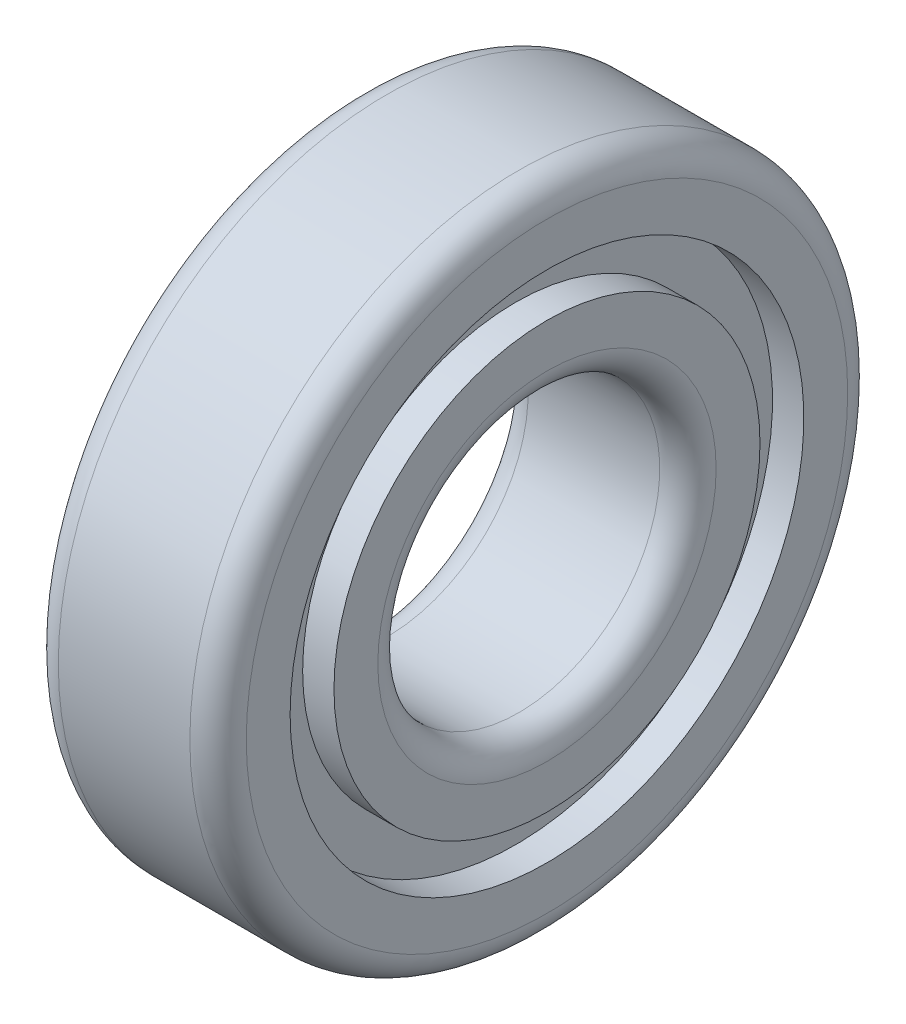
SolidWorks part; units mm, degrees
material "AISI 1020"
ref_plane "Спереди" through (0, 0, 0) normal (0, 0, 1) x (1, 0, 0)
ref_plane "Сверху" through (0, 0, 0) normal (0, 1, 0) x (1, 0, 0)
ref_plane "Справа" through (0, 0, 0) normal (1, 0, 0) x (0, 0, -1)
sketch "Эскиз1" plane through (0, 0, 0) normal (0, 0, 1) x (1, 0, 0)
  line L0 (-1000, 0) -> (49000, 0) construction
  line L1 (0, -1000) -> (0, 49000) construction
  line L2 (0.7, 1.5) -> (-0.7, 1.5)
  line L3 (-1, 1.8) -> (-1, 2.2667)
  line L4 (-1, 2.2667) -> (-0.6667, 2.2667)
  line L5 (-0.6667, 2.2667) -> (-0.6667, 2.7333)
  line L6 (-0.6667, 2.7333) -> (-1, 2.7333)
  line L7 (-1, 2.7333) -> (-1, 3.2)
  line L8 (-0.7, 3.5) -> (0.7, 3.5)
  line L9 (1, 2.7333) -> (1, 3.2)
  line L10 (0.6667, 2.7333) -> (1, 2.7333)
  line L11 (0.6667, 2.2667) -> (0.6667, 2.7333)
  line L12 (1, 2.2667) -> (0.6667, 2.2667)
  line L13 (1, 1.8) -> (1, 2.2667)
  arc A0 (-0.7, 1.5) -> (-1, 1.8) centre (-0.7, 1.8) cw
  arc A1 (-1, 3.2) -> (-0.7, 3.5) centre (-0.7, 3.2) cw
  arc A2 (1, 3.2) -> (0.7, 3.5) centre (0.7, 3.2) ccw
  arc A3 (0.7, 1.5) -> (1, 1.8) centre (0.7, 1.8) ccw
  point P23 (0, 3.5)
  point P27 (0, 1.5)
  dimension "_r" = 0.3
  dimension "_d" = 3
  dimension "D" = 7
  dimension "B" = 2
  dimension "D2" = 1.3333
revolve "Повернуть1" add sketch "Эскиз1" angle 360 about L0
equation "\"D2@Эскиз1\"= \"B@Эскиз1\" / 3 * 2"
